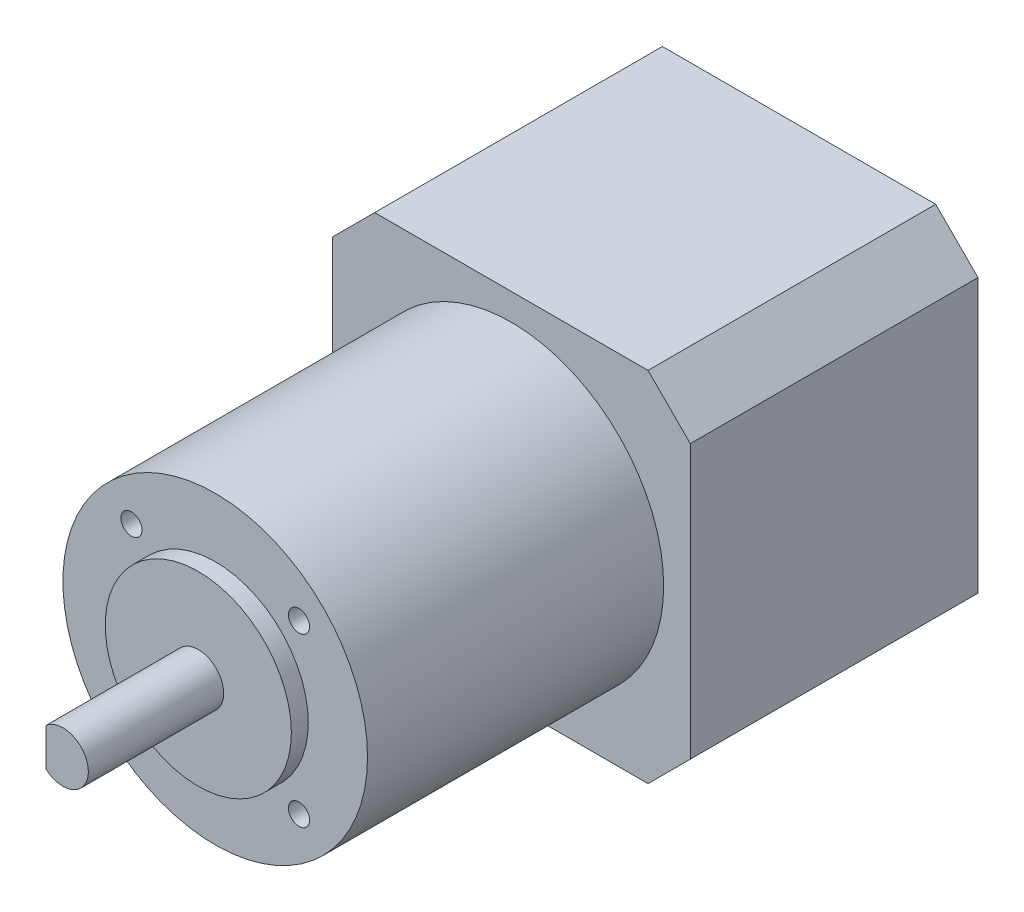
SolidWorks part; units mm, degrees
ref_plane "Front Plane" through (0, 0, 0) normal (0, 0, 1) x (1, 0, 0)
ref_plane "Top Plane" through (0, 0, 0) normal (0, 1, 0) x (1, 0, 0)
ref_plane "Right Plane" through (0, 0, 0) normal (1, 0, 0) x (0, 0, -1)
sketch "Sketch1" plane through (0, 0, 0) normal (0, 0, 1) x (1, 0, 0)
  line L1 (-21.15, -21.15) -> (21.15, -21.15)
  line L2 (-21.15, -21.15) -> (-21.15, 21.15)
  line L3 (-21.15, 21.15) -> (21.15, 21.15)
  line L4 (21.15, -21.15) -> (21.15, 21.15)
  line L5 (-21.15, -21.15) -> (21.15, 21.15) construction
  line L6 (-21.15, 21.15) -> (21.15, -21.15) construction
  point P0 (0, 0)
  dimension "D1" = 42.3
extrude "Boss-Extrude1" add sketch "Sketch1" along normal blind 34 contours L3 L4 L1 L2
sketch "Sketch2" plane through (0, 0, 34) normal (0, 0, 1) x (1, 0, 0)
  circle A0 centre (0, 0) radius 18
  dimension "D1" = 36
extrude "Boss-Extrude2" add sketch "Sketch2" along normal blind 35
sketch "Sketch3" plane through (0, 0, 69) normal (0, 0, 1) x (1, 0, 0)
  circle A0 centre (0, 0) radius 11
  dimension "D1" = 22
extrude "Boss-Extrude3" add sketch "Sketch3" along normal blind 2
sketch "Sketch4" plane through (0, 0, 71) normal (0, 0, 1) x (1, 0, 0)
  circle A0 centre (0, 0) radius 3
  dimension "D1" = 6
extrude "Boss-Extrude4" add sketch "Sketch4" along normal blind 16
sketch "Sketch5" plane through (0, 0, 87) normal (0, 0, 1) x (1, 0, 0)
  line L0 (-2, 2.2361) -> (-2, -2.2361)
  circle A0 centre (0, 0) radius 3 construction
  circle A1 centre (0, 0) radius 3
  arc A2 (-2, 2.2361) -> (-2, -2.2361) centre (0, 0) ccw
  circle A3 centre (0, 0) radius 3 construction
  point P4 (3, 0)
  dimension "D2" = 5
  dimension "D1" = 0
extrude "Cut-Extrude1" cut sketch "Sketch5" against normal blind 12
chamfer "Chamfer1" distance 5 angle 45 4 edges at (-21.15, -21.15, 17) (21.15, -21.15, 17) (-21.15, 21.15, 17) (21.15, 21.15, 17)
sketch "Sketch6" plane through (0, 0, 69) normal (0, 0, 1) x (1, 0, 0)
  line L1 (9.8995, -9.8995) -> (-9.8995, -9.8995) construction
  line L2 (9.8995, -9.8995) -> (9.8995, 9.8995) construction
  line L3 (9.8995, 9.8995) -> (-9.8995, 9.8995) construction
  line L4 (-9.8995, -9.8995) -> (-9.8995, 9.8995) construction
  line L5 (9.8995, -9.8995) -> (-9.8995, 9.8995) construction
  line L6 (9.8995, 9.8995) -> (-9.8995, -9.8995) construction
  point P0 (0, 0)
  dimension "D1" = 28
hole_wizard "M3x0.5 Tapped Hole1" positions "Sketch7" profile "Sketch8" tap size "M3x0.5" standard "ANSI Metric"
sketch "Sketch7" plane through (0, 0, 69) normal (0, 0, 1) x (1, 0, 0)
  point P0 (-9.8995, 9.8995)
  point P5 (9.8995, 9.8995)
  point P8 (9.8995, -9.8995)
  point P10 (-9.8995, -9.8995)
sketch "Sketch8" plane through (-9.8995, 9.8995, 69) normal (1, 0, 0) x (0, -1, 0)
  line L0 (0, 0) -> (0, 8.2511)
  line L1 (0, 8.2511) -> (1.25, 7.5)
  line L2 (1.25, 7.5) -> (1.25, 0)
  line L5 (1.25, 0) -> (0, 0)
  line L10 (0, 8.2511) -> (-1.25, 7.5) construction
  line L11 (0, -6.35) -> (0, 107.95) construction
  dimension "Tap Drill Dia." = 2.5
  dimension "Tap Drill Depth" = 7.5
  dimension "Drill Angle" = 118
cosmetic thread "Hole Thread1" parameters "D1"=6, "D2"=3
cosmetic thread "Hole Thread2" parameters "D1"=6, "D2"=3
cosmetic thread "Hole Thread3" parameters "D1"=6, "D2"=3
cosmetic thread "Hole Thread4" parameters "D1"=6, "D2"=3
